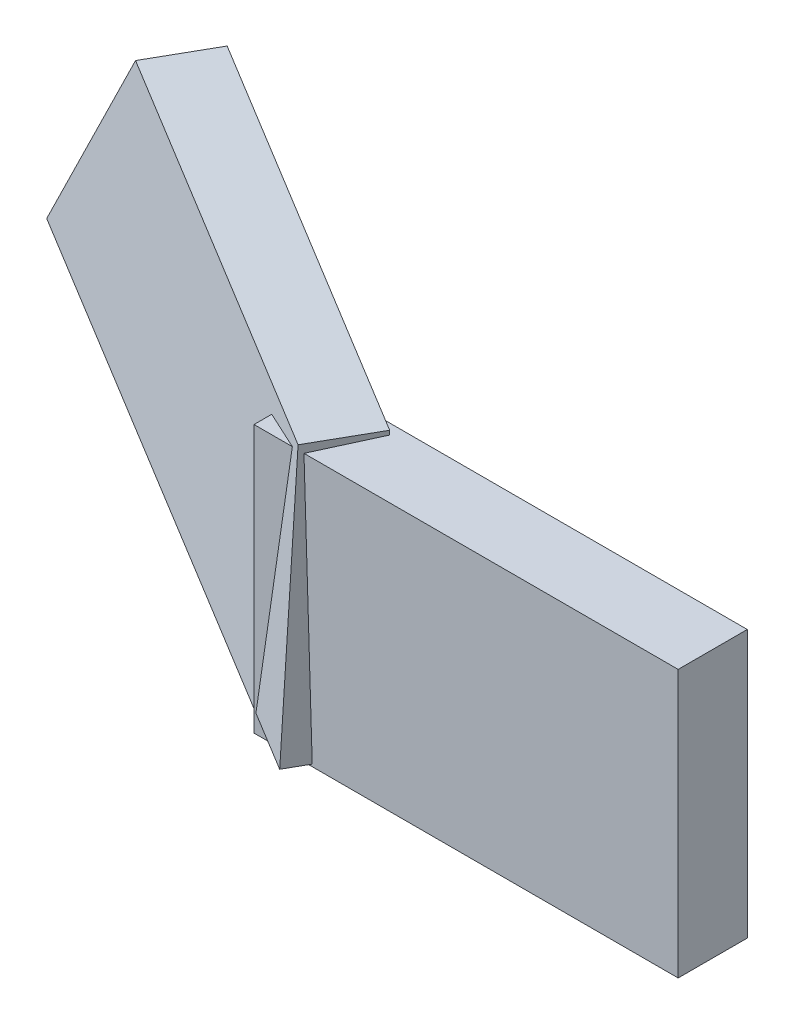
SolidWorks part; units mm, degrees
ref_plane "Front Plane" through (0, 0, 0) normal (0, 0, 1) x (1, 0, 0)
ref_plane "Top Plane" through (0, 0, 0) normal (0, 1, 0) x (1, 0, 0)
ref_plane "Right Plane" through (0, 0, 0) normal (1, 0, 0) x (0, 0, -1)
sketch "Sketch1" plane through (0, 0, 0) normal (0, 0, 1) x (1, 0, 0)
  line L1 (7.247, 29.6593) -> (-54.098, 29.6593)
  line L2 (7.247, 29.6593) -> (7.247, -8.9982)
  line L3 (7.247, -8.9982) -> (-54.098, -8.9982)
  line L4 (-54.098, 29.6593) -> (-54.098, -8.9982)
extrude "Boss-Extrude1" add sketch "Sketch1" along normal blind 10
sketch "Sketch2" plane through (-8.8873, 1.3003, 19.2214) normal (-0.4189, 0.0613, 0.906) x (0.908, 0.0283, 0.4179)
  line L1 (-87.6845, 45.8881) -> (-37.5454, 30.0821)
  line L4 (-37.5454, 30.0821) -> (-37.5454, -9.3271)
  line L5 (-109.4217, 13.3313) -> (-87.6845, 45.8881)
  line L6 (-37.5454, -9.3271) -> (-109.4217, 13.3313)
  line L7 (-46.163, 0.054) -> (-94.2979, 15.2281) construction
extrude "Boss-Extrude2" add sketch "Sketch2" along normal blind 10
sketch "Sketch3" plane through (0, 0, 0) normal (0, -1, 0) x (1, 0, 0)
  line L1 (2.7655, -3.5557) -> (-52.8877, -3.5557)
  line L2 (2.7655, -3.5557) -> (2.7655, 1.1121)
  line L3 (2.7655, 1.1121) -> (-52.8877, 1.1121)
  line L4 (-52.8877, -3.5557) -> (-52.8877, 1.1121)
extrude "Boss-Extrude3" add sketch "Sketch3" along normal blind 3
ref_plane "Plane1" through (-47.105, 23, -0.8) normal (0.866, -0.273, 0.4189) x (0.3995, -0.1259, -0.908)
sketch "Sketch5" plane through (-3.7751, -13.2754, -0.8474) normal (-0.273, -0.9601, -0.0613) x (0.962, -0.2725, -0.0174)
  line L0 (-47.1036, 2.2896) -> (-100.8463, -21.7758)
  line L3 (-47.1036, 2.2896) -> (-46.8565, 2.2896)
  line L5 (-100.8463, -21.7758) -> (-98.6382, -26.8874)
  line L8 (-46.8565, 2.2896) -> (-46.8565, -2.5426)
  line L9 (-46.8565, -2.5426) -> (-98.6382, -26.8874)
extrude "Boss-Extrude4" add sketch "Sketch5" along normal blind 3
